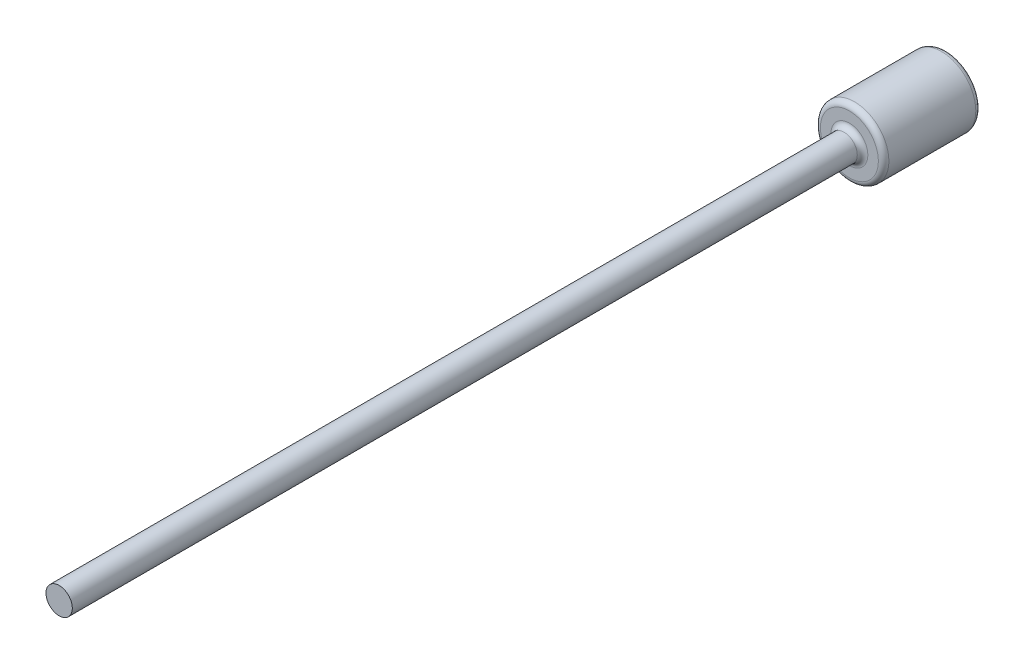
SolidWorks part; units mm, degrees
material "Chrome Stainless Steel"
ref_plane "Front Plane" through (0, 0, 0) normal (0, 0, 1) x (1, 0, 0)
ref_plane "Top Plane" through (0, 0, 0) normal (0, 1, 0) x (1, 0, 0)
ref_plane "Right Plane" through (0, 0, 0) normal (1, 0, 0) x (0, 0, -1)
sketch "Sketch1" plane through (0, 0, 0) normal (0, 0, 1) x (1, 0, 0)
  circle A0 centre (0, 0) radius 13
  dimension "D1" = 26
extrude "Boss-Extrude1" add sketch "Sketch1" against normal blind 37
sketch "Sketch2" plane through (0, 0, 0) normal (0, 0, 1) x (1, 0, 0)
  circle A0 centre (0, 0) radius 5
  dimension "D1" = 10
extrude "Boss-Extrude2" add sketch "Sketch2" along normal blind 280
sketch "Sketch3" plane through (0, 0, 280) normal (0, 0, 1) x (1, 0, 0)
  circle A0 centre (0, 0) radius 5
  dimension "D1" = 10
extrude "Boss-Extrude3" add sketch "Sketch3" along normal blind 20
fillet "Fillet1" radius 2 3 edges at (13, 0, -37) (13, 0, 0) (5, 0, 0)
